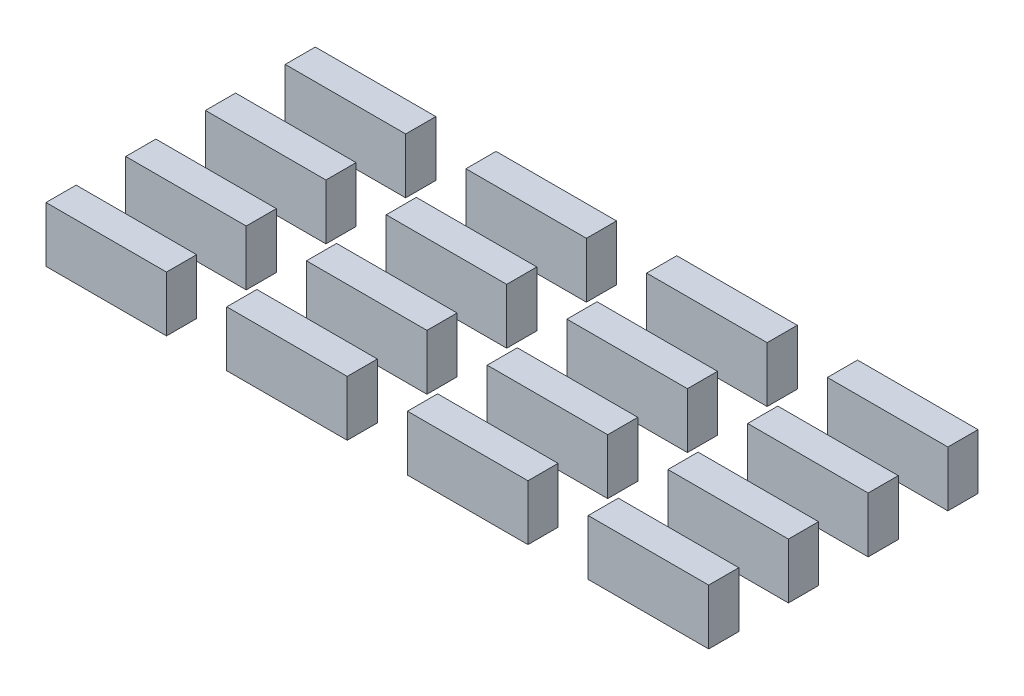
SolidWorks part; units mm, degrees
ref_plane "Front Plane" through (0, 0, 0) normal (0, 0, 1) x (1, 0, 0)
ref_plane "Top Plane" through (0, 0, 0) normal (0, 1, 0) x (1, 0, 0)
ref_plane "Right Plane" through (0, 0, 0) normal (1, 0, 0) x (0, 0, -1)
sketch "Sketch1" plane through (0, 0, 0) normal (0, 1, 0) x (1, 0, 0)
  line L0 (31, 8.5) -> (47, 8.5)
  line L1 (0, 0) -> (102, 0) construction
  line L2 (0, 0) -> (0, 53) construction
  line L3 (0, 53) -> (102, 53) construction
  line L4 (102, 0) -> (102, 53) construction
  line L5 (7, 8.5) -> (23, 8.5)
  line L6 (7, 8.5) -> (7, 12.5)
  line L7 (7, 12.5) -> (23, 12.5)
  line L8 (23, 8.5) -> (23, 12.5)
  line L9 (31, 8.5) -> (31, 12.5)
  line L10 (31, 12.5) -> (47, 12.5)
  line L11 (47, 8.5) -> (47, 12.5)
  line L12 (55, 8.5) -> (71, 8.5)
  line L13 (55, 8.5) -> (55, 12.5)
  line L14 (55, 12.5) -> (71, 12.5)
  line L15 (71, 8.5) -> (71, 12.5)
  line L16 (79, 8.5) -> (95, 8.5)
  line L17 (79, 8.5) -> (79, 12.5)
  line L18 (79, 12.5) -> (95, 12.5)
  line L19 (95, 8.5) -> (95, 12.5)
  line L20 (7, 19.0875) -> (23, 19.0875)
  line L21 (7, 19.0875) -> (7, 23.0875)
  line L22 (7, 23.0875) -> (23, 23.0875)
  line L23 (23, 19.0875) -> (23, 23.0875)
  line L24 (31, 19.0875) -> (47, 19.0875)
  line L25 (31, 19.0875) -> (31, 23.0875)
  line L26 (31, 23.0875) -> (47, 23.0875)
  line L27 (47, 19.0875) -> (47, 23.0875)
  line L28 (55, 19.0875) -> (71, 19.0875)
  line L29 (55, 19.0875) -> (55, 23.0875)
  line L30 (55, 23.0875) -> (71, 23.0875)
  line L31 (71, 19.0875) -> (71, 23.0875)
  line L32 (79, 19.0875) -> (95, 19.0875)
  line L33 (79, 19.0875) -> (79, 23.0875)
  line L34 (79, 23.0875) -> (95, 23.0875)
  line L35 (95, 19.0875) -> (95, 23.0875)
  line L36 (7, 29.675) -> (23, 29.675)
  line L37 (7, 29.675) -> (7, 33.675)
  line L38 (7, 33.675) -> (23, 33.675)
  line L39 (23, 29.675) -> (23, 33.675)
  line L40 (31, 29.675) -> (47, 29.675)
  line L41 (31, 29.675) -> (31, 33.675)
  line L42 (31, 33.675) -> (47, 33.675)
  line L43 (47, 29.675) -> (47, 33.675)
  line L44 (55, 29.675) -> (71, 29.675)
  line L45 (55, 29.675) -> (55, 33.675)
  line L46 (55, 33.675) -> (71, 33.675)
  line L47 (71, 29.675) -> (71, 33.675)
  line L48 (79, 29.675) -> (95, 29.675)
  line L49 (79, 29.675) -> (79, 33.675)
  line L50 (79, 33.675) -> (95, 33.675)
  line L51 (95, 29.675) -> (95, 33.675)
  line L52 (7, 40.2625) -> (23, 40.2625)
  line L53 (7, 40.2625) -> (7, 44.2625)
  line L54 (7, 44.2625) -> (23, 44.2625)
  line L55 (23, 40.2625) -> (23, 44.2625)
  line L56 (31, 40.2625) -> (47, 40.2625)
  line L57 (31, 40.2625) -> (31, 44.2625)
  line L58 (31, 44.2625) -> (47, 44.2625)
  line L59 (47, 40.2625) -> (47, 44.2625)
  line L60 (55, 40.2625) -> (71, 40.2625)
  line L61 (55, 40.2625) -> (55, 44.2625)
  line L62 (55, 44.2625) -> (71, 44.2625)
  line L63 (71, 40.2625) -> (71, 44.2625)
  line L64 (79, 40.2625) -> (95, 40.2625)
  line L65 (79, 40.2625) -> (79, 44.2625)
  line L66 (79, 44.2625) -> (95, 44.2625)
  line L67 (95, 40.2625) -> (95, 44.2625)
  dimension "D2" = 4
extrude "Boss-Extrude1" add sketch "Sketch1" against normal blind 7.35
